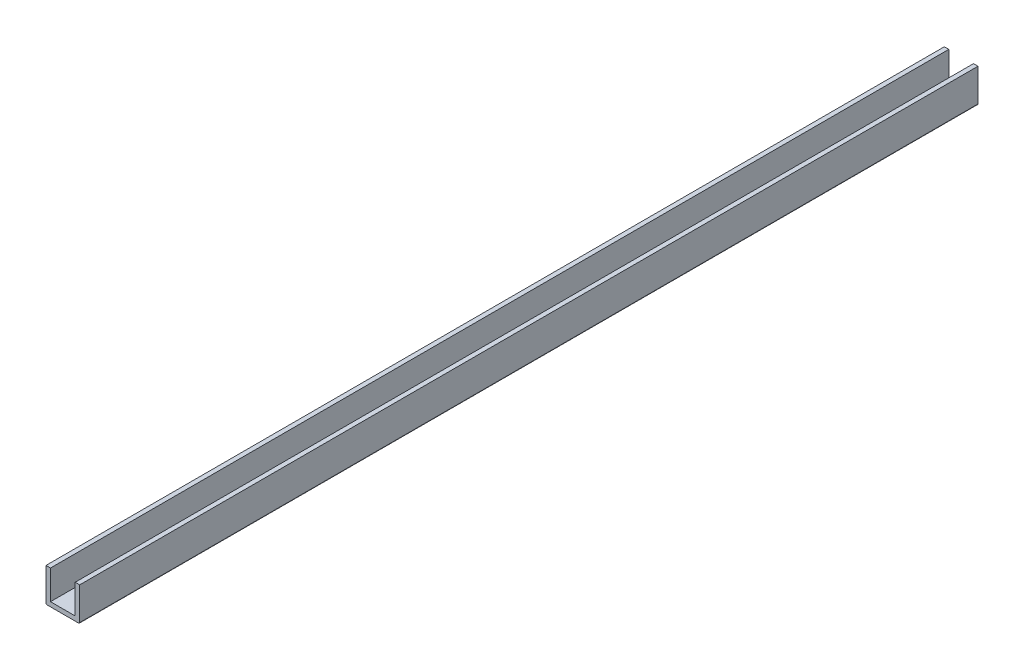
SolidWorks part; units mm, degrees
ref_plane "Alzado" through (0, 0, 0) normal (0, 0, 1) x (1, 0, 0)
ref_plane "Planta" through (0, 0, 0) normal (0, 1, 0) x (1, 0, 0)
ref_plane "Vista lateral" through (0, 0, 0) normal (1, 0, 0) x (0, 0, -1)
sketch "Croquis1" plane through (0, 0, 0) normal (0, 0, 1) x (1, 0, 0)
  line L0 (-7.5, 15) -> (-7.5, 0)
  line L1 (-7.5, 0) -> (7.5, 0)
  line L2 (7.5, 0) -> (7.5, 15)
  line L3 (7.5, 15) -> (5.5, 15)
  line L4 (5.5, 15) -> (5.5, 2)
  line L5 (5.5, 2) -> (-5.5, 2)
  line L6 (-5.5, 2) -> (-5.5, 15)
  line L7 (-5.5, 15) -> (-7.5, 15)
  line L8 (0, 19.1935) -> (0, -16.3914) construction
  dimension "D1" = 2
  dimension "D2" = 15
  dimension "D3" = 15
  dimension "D4" = 2
extrude "Saliente-Extruir1" add sketch "Croquis1" along normal blind 400
fillet "Redondeo1" radius 0.5 2 edges at (7.5, 0, 200) (-7.5, 0, 200)
sketch "Croquis2" plane through (0, 0, 0) normal (0, -1, 0) x (1, 0, 0)
  line L0 (0, -11.4462) -> (0, 425.0133) construction
  line L2 (-7, 400) -> (7, 400) construction
  line L3 (-7, 0) -> (7, 0) construction
  circle A0 centre (0, 280) radius 2
  circle A1 centre (0, 330) radius 2
  circle A2 centre (0, 390) radius 1.75
  circle A3 centre (0, 380) radius 1.75
  circle A4 centre (0, 10) radius 1.75
  circle A5 centre (0, 20) radius 1.75
  circle A6 centre (0, 230) radius 2
  circle A7 centre (0, 180) radius 2
  circle A8 centre (0, 130) radius 2
  circle A9 centre (0, 80) radius 2
  circle A10 centre (0, 30) radius 2
  dimension "D1" = 4
  dimension "D4" = 3.5
  dimension "D2" = 10
  dimension "D3" = 50
  dimension "D5" = 10
  dimension "D6" = 10
  dimension "D7" = 10
  dimension "D8" = 50
  dimension "D9" = 50
  dimension "D10" = 50
  dimension "D11" = 50
  dimension "D12" = 50
  dimension "D13" = 50
extrude "Cortar-Extruir1" cut sketch "Croquis2" against normal through all
